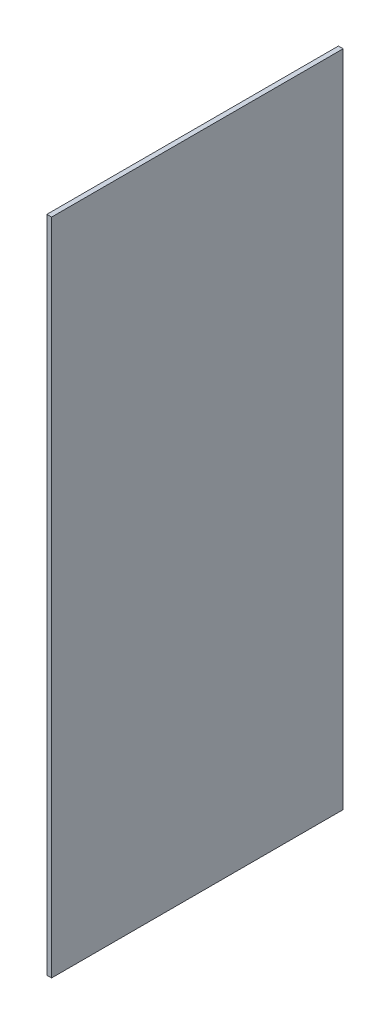
SolidWorks part; units mm, degrees
material "6061 Alloy"
ref_plane "Front Plane" through (0, 0, 0) normal (0, 0, 1) x (1, 0, 0)
ref_plane "Top Plane" through (0, 0, 0) normal (0, 1, 0) x (1, 0, 0)
ref_plane "Right Plane" through (0, 0, 0) normal (1, 0, 0) x (0, 0, -1)
sketch "Sketch2" plane through (0, 0, 0) normal (1, 0, 0) x (0, 0, -1)
  line L1 (-50, 113) -> (50, 113)
  line L2 (-50, 113) -> (-50, -113)
  line L3 (-50, -113) -> (50, -113)
  line L4 (50, 113) -> (50, -113)
  line L5 (-50, 113) -> (50, -113) construction
  line L6 (-50, -113) -> (50, 113) construction
  point P0 (0, 0)
  dimension "D1" = 226
  dimension "D2" = 100
extrude "Boss-Extrude1" add sketch "Sketch2" along normal blind 1.6256
